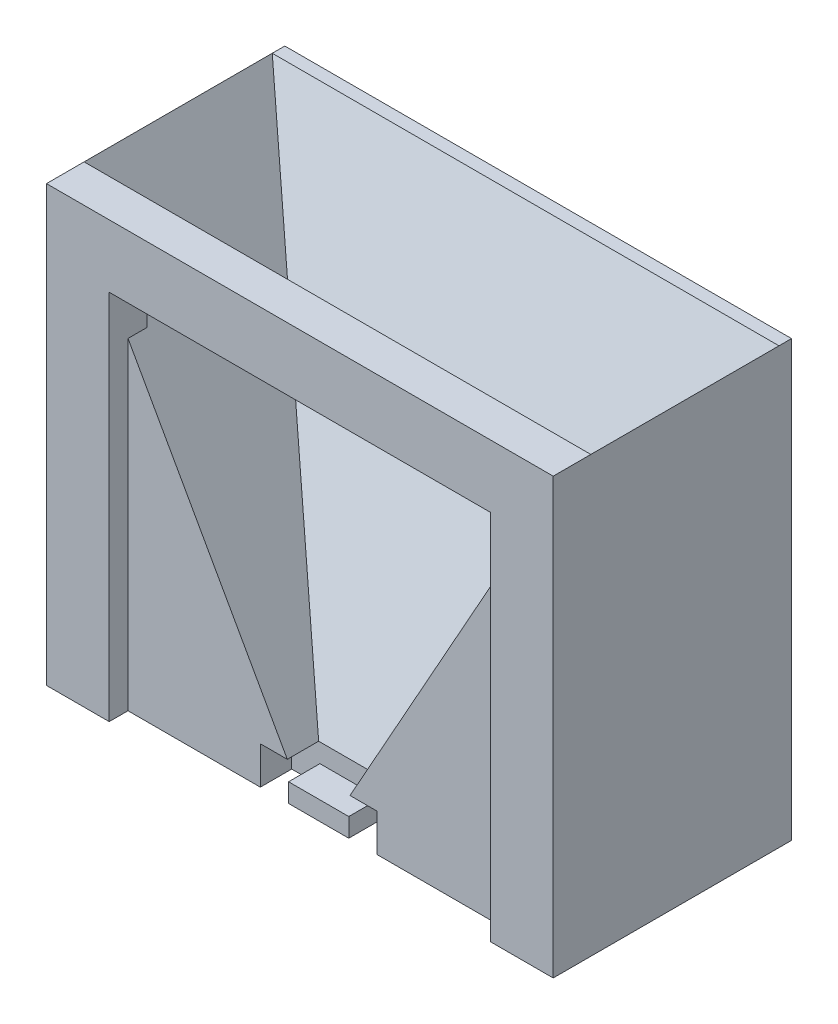
SolidWorks part; units mm, degrees
material "ABS"
ref_plane "Front Plane" through (0, 0, 0) normal (0, 0, 1) x (1, 0, 0)
ref_plane "Top Plane" through (0, 0, 0) normal (0, 1, 0) x (1, 0, 0)
ref_plane "Right Plane" through (0, 0, 0) normal (1, 0, 0) x (0, 0, -1)
sketch "Sketch1" plane through (0, 0, 0) normal (0, 0, 1) x (1, 0, 0)
  line L0 (30.4, -26.4) -> (40.4, -26.4)
  line L1 (-30.4, -26.4) -> (-40.4, -26.4)
  line L7 (-30.4, -26.4) -> (-30.4, 31.4)
  line L8 (-30.4, 31.4) -> (30.4, 31.4)
  line L9 (30.4, -26.4) -> (30.4, 31.4)
  line L10 (-40.4, -26.4) -> (-40.4, 41.4)
  line L11 (-40.4, 41.4) -> (40.4, 41.4)
  line L12 (40.4, -26.4) -> (40.4, 41.4)
extrude "Boss-Extrude1" add sketch "Sketch1" against normal blind 3
sketch "Sketch5" plane through (0, 0, 0) normal (0, 0, 1) x (1, 0, 0)
  line L0 (-40.4, 41.4) -> (-5, -21.9)
  line L1 (40.4, 41.4) -> (5, -21.9)
  line L2 (0, -21.9) -> (5, -21.9)
  line L3 (0, -21.9) -> (-5, -21.9)
  line L4 (40.4, -26.4) -> (40.4, 41.4) construction
  line L5 (40.4, -27.9) -> (-40.4, -27.9)
  line L6 (-40.4, 41.4) -> (-40.4, -26.4) construction
  line L7 (-40.4, -27.9) -> (-40.4, 41.4)
  line L8 (40.4, 41.4) -> (40.4, -27.9)
extrude "Boss-Extrude5" add sketch "Sketch5" against normal blind 35
sketch "Sketch6" plane through (0, 0, 0) normal (0, 0, 1) x (1, 0, 0)
  line L0 (-40.4, 41.4) -> (40.4, 41.4)
  line L1 (40.4, 41.4) -> (40.4, -27.9)
  line L2 (-40.4, 41.4) -> (-40.4, -27.9)
  line L3 (-30.4, 31.4) -> (-30.4, -27.9)
  line L6 (30.4, 31.4) -> (-30.4, 31.4)
  line L7 (30.4, 31.4) -> (30.4, -27.9)
  line L9 (40.4, -27.9) -> (30.4, -27.9)
  line L10 (-40.4, -27.9) -> (-30.4, -27.9)
extrude "Boss-Extrude6" add sketch "Sketch6" along normal blind 3
sketch "Sketch8" plane through (0, 0, -35) normal (0, 0, -1) x (-1, 0, 0)
  line L1 (-40.4, 41.4) -> (40.4, 41.4)
  line L2 (-40.4, 41.4) -> (-40.4, -27.9)
  line L3 (-40.4, -27.9) -> (40.4, -27.9)
  line L4 (40.4, 41.4) -> (40.4, -27.9)
extrude "Boss-Extrude8" add sketch "Sketch8" against normal blind 2
sketch "Sketch9" plane through (40.4, 0, 0) normal (1, 0, 0) x (0, 0, -1)
  line L5 (33, -21.9) -> (33, 41.4)
  line L8 (5, -21.9) -> (33, -21.9)
  line L9 (5, -21.9) -> (33, 41.4)
extrude "Boss-Extrude9" add sketch "Sketch9" against normal blind 80.8
sketch "Sketch10" plane through (0, 0, 0) normal (0, 0, 1) x (1, 0, 0)
  line L4 (-30.4, -27.9) -> (30.4, -27.9) construction
  line L15 (9.3, -27.9) -> (9.3, -21.9)
  line L16 (-9.3, -27.9) -> (-9.3, -21.9)
  line L19 (-9.3, -21.9) -> (-4.8, -21.9)
  line L20 (5, -21.9) -> (-5, -21.9) construction
  line L21 (-4.8, -21.9) -> (-4.8, -27.9)
  line L22 (-4.8, -27.9) -> (-9.3, -27.9)
  line L23 (9.3, -21.9) -> (4.8, -21.9)
  line L24 (4.8, -21.9) -> (4.8, -27.9)
  line L25 (4.8, -27.9) -> (9.3, -27.9)
extrude "Cut-Extrude1" cut sketch "Sketch10" against normal blind 5
sketch "Sketch13" plane through (0, 0, -5) normal (0, 0, 1) x (1, 0, 0)
  line L10 (-5, -21.9) -> (4.8, -21.9)
  line L17 (-5, -21.9) -> (-5, -24.9)
  line L20 (-5, -24.9) -> (4.8, -24.9)
  line L21 (4.8, -24.9) -> (4.8, -21.9)
extrude "Cut-Extrude2" cut sketch "Sketch13" along normal up to surface (5 mm away) up to face at (16.88, -15.2163, 0)
